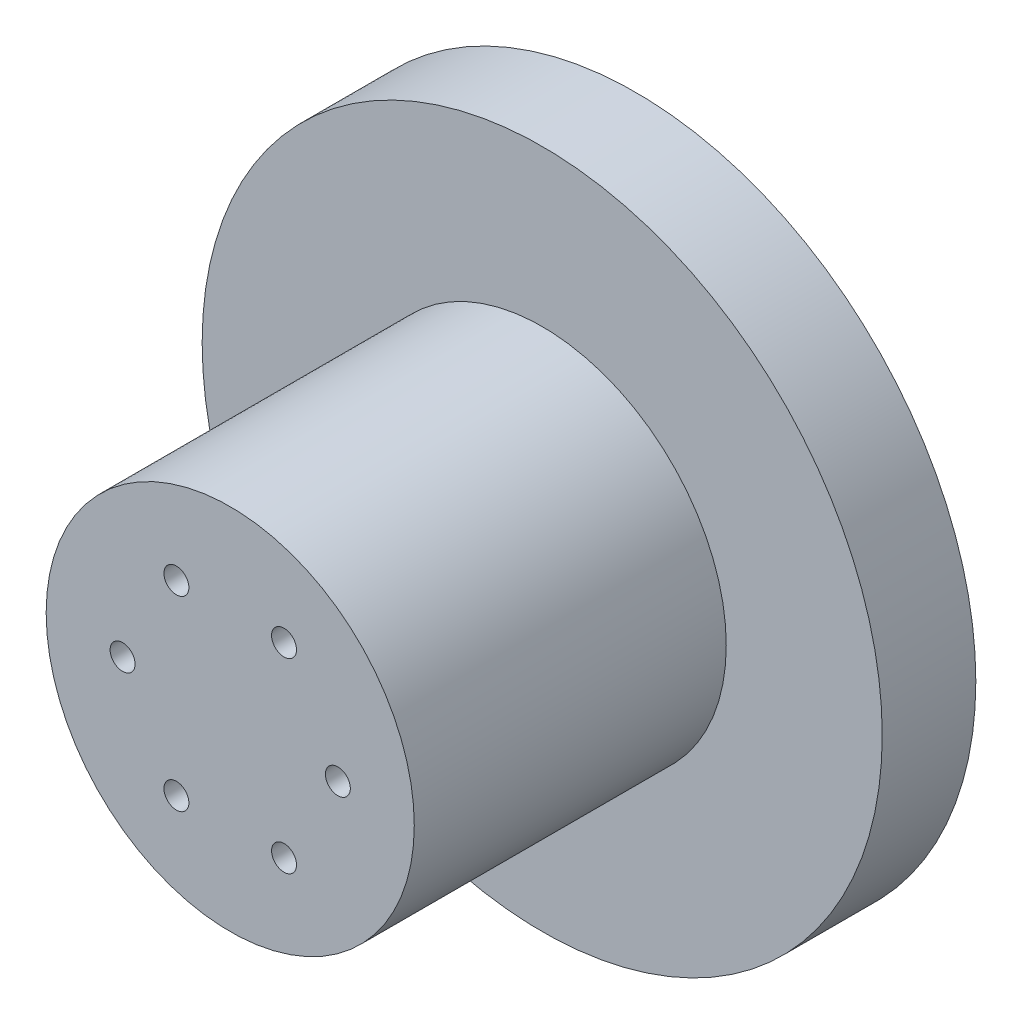
SolidWorks part; units mm, degrees
ref_plane "前视基准面" through (0, 0, 0) normal (0, 0, 1) x (1, 0, 0)
ref_plane "上视基准面" through (0, 0, 0) normal (0, 1, 0) x (1, 0, 0)
ref_plane "右视基准面" through (0, 0, 0) normal (1, 0, 0) x (0, 0, -1)
other "Configuration Table"
sketch "草图1" plane through (0, 0, 0) normal (0, 0, 1) x (1, 0, 0)
  circle A0 centre (0, 0) radius 29.5
extrude "凸台-拉伸1" add sketch "草图1" along normal blind 50
shell "抽壳2" thickness 4
sketch "草图3" plane through (0, 0, 50) normal (0, 0, 1) x (1, 0, 0)
  circle A0 centre (-17.25, 0) radius 2
  circle A1 centre (-8.625, 14.9389) radius 2
  circle A2 centre (8.625, 14.9389) radius 2
  circle A3 centre (17.25, 0) radius 2
  circle A4 centre (8.625, -14.9389) radius 2
  circle A5 centre (-8.625, -14.9389) radius 2
  point P15 (0, 0)
  dimension "D1" = 17.25
  dimension "D2" = 6
extrude "切除-拉伸1" cut sketch "草图3" against normal through all
sketch "草图5" plane through (0, 0, 0) normal (0, 0, -1) x (-1, 0, 0)
  circle A0 centre (0, 0) radius 25.5 construction
  circle A1 centre (0, 0) radius 29.5
  circle A2 centre (0, 0) radius 29.5
  circle A3 centre (0, 0) radius 25.5
  circle A4 centre (0, 0) radius 54.5
  circle M3 centre (0, 0) radius 25.5
  circle M4 centre (0, 0) radius 29.5
  dimension "D1" = 0
  dimension "D2" = 29
extrude "凸台-拉伸7" add sketch "草图5" along normal blind 15 contours A4 M4 | M4 M3
sketch "草图6" plane through (0, 0, -15) normal (0, 0, -1) x (-1, 0, 0)
  line L0 (0, 0) -> (-55.8933, 0) construction
  circle A2 centre (-42, 0) radius 2
  circle A3 centre (42, 0) radius 2
  point P3 (0, 0)
  point P6 (0, 0)
  point P8 (0, 0)
  dimension "D1" = 42
  dimension "42" = 42
extrude "切除-拉伸3" cut sketch "草图6" against normal blind 4
